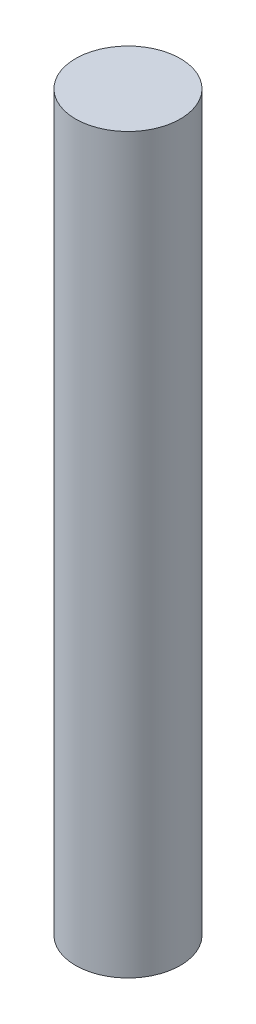
SolidWorks part; units mm, degrees
ref_plane "Front Plane" through (0, 0, 0) normal (0, 0, 1) x (1, 0, 0)
ref_plane "Top Plane" through (0, 0, 0) normal (0, 1, 0) x (1, 0, 0)
ref_plane "Right Plane" through (0, 0, 0) normal (1, 0, 0) x (0, 0, -1)
sketch "Sketch1" plane through (0, 0, 0) normal (0, 1, 0) x (1, 0, 0)
  circle A0 centre (0, 0) radius 1
extrude "Boss-Extrude1" add sketch "Sketch1" along normal blind 14
